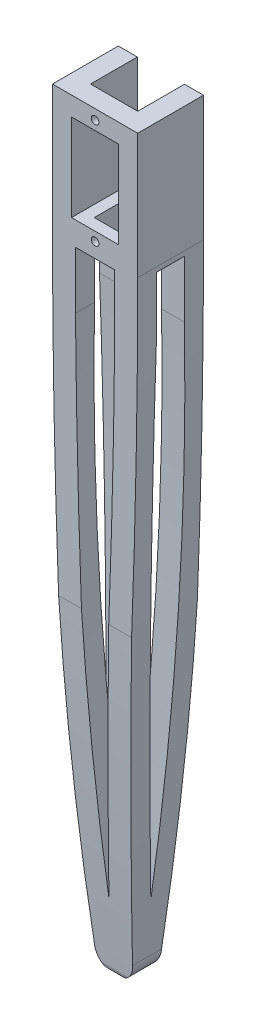
SolidWorks part; units mm, degrees
ref_plane "Front Plane" through (0, 0, 0) normal (0, 0, 1) x (1, 0, 0)
ref_plane "Top Plane" through (0, 0, 0) normal (0, 1, 0) x (1, 0, 0)
ref_plane "Right Plane" through (0, 0, 0) normal (1, 0, 0) x (0, 0, -1)
sketch "Sketch1" plane through (0, 0, 0) normal (0, 0, 1) x (1, 0, 0)
  line L0 (0, -16.45) -> (0, -173.55) construction
  line L1 (-6.2, 16.45) -> (6.2, 16.45)
  line L2 (-11.2, 11.45) -> (-11.2, -16.45)
  line L4 (11.2, 11.45) -> (11.2, -16.45)
  line L5 (-11.2, 16.45) -> (11.2, -16.45) construction
  line L6 (-11.2, -16.45) -> (11.2, 16.45) construction
  arc A1 (-5, -178.55) -> (5, -178.55) centre (0, -178.55) ccw
  arc A2 (-11.2, -16.45) -> (-5, -178.55) centre (2110.9653, -16.45) ccw
  arc A3 (11.2, -16.45) -> (5, -178.55) centre (-2110.9653, -16.45) cw
  arc A4 (11.2, 11.45) -> (6.2, 16.45) centre (6.2, 11.45) ccw
  arc A5 (-6.2, 16.45) -> (-11.2, 11.45) centre (-6.2, 11.45) ccw
  point P0 (0, 0)
  dimension "D4" = 5
  dimension "D1" = 32.9
  dimension "D2" = 22.4
  dimension "D3" = 162.1
extrude "Boss-Extrude2" add sketch "Sketch1" along normal blind 5
sketch "Sketch4" plane through (0, 0, 5) normal (0, 0, 1) x (1, 0, 0)
  line L1 (-6.2, 11.45) -> (6.2, 11.45)
  line L2 (-6.2, 11.45) -> (-6.2, -11.45)
  line L3 (-6.2, -11.45) -> (6.2, -11.45)
  line L4 (6.2, 11.45) -> (6.2, -11.45)
  line L5 (-6.2, 11.45) -> (6.2, -11.45) construction
  line L6 (-6.2, -11.45) -> (6.2, 11.45) construction
  point P0 (0, 0)
  dimension "D1" = 22.9
  dimension "D2" = 12.4
extrude "Cut-Extrude1" cut sketch "Sketch4" against normal blind 5
sketch "Sketch5" plane through (0, 0, 5) normal (0, 0, 1) x (1, 0, 0)
  line L0 (0, 0) -> (0, 13.8) construction
  line L1 (0, 0) -> (0, -13.8) construction
  circle A0 centre (0, 13.8) radius 1
  circle A1 centre (0, -13.8) radius 1
  dimension "D1" = 13.8
  dimension "D2" = 13.8
extrude "Cut-Extrude2" cut sketch "Sketch5" against normal blind 5
sketch3d "3DSketch1"
  line L6 (-5.1604, -32.6864, 5) -> (5.1604, -32.6864, 5)
  spline S2 degree 5 poles (-5.1604, -32.6864, 5) (-5.1261, -37.5289, 5) (-5.0708, -42.3713, 5) (-4.9981, -47.2135, 5) (-4.7659, -60.1446, 5) (-4.4569, -73.0738, 5) (-4.2293, -81.1606, 5) (-3.6967, -97.3316, 5) (-2.9925, -113.496, 5) (-2.6018, -121.5766, 5) (-1.8933, -135.0415, 5) (-1.1015, -148.5022, 5) (-0.7667, -153.8853, 5) (-0.4048, -159.3358, 5) (-0.0148, -164.7842, 5) (-0.0099, -164.8531, 5) (-0.0049, -164.922, 5) (0, -164.9909, 5) knots 0.10922 0.10922 0.10922 0.10922 0.10922 0.10922 0.272094 0.272094 0.272094 0.544187 0.544187 0.544187 0.816281 0.816281 0.816281 0.997676 0.997676 0.997676 1 1 1 1 1 1
  spline S3 degree 5 poles (0, -164.9909, 5) (0.0049, -164.922, 5) (0.0099, -164.8531, 5) (0.0148, -164.7842, 5) (0.4048, -159.3358, 5) (0.7667, -153.8853, 5) (1.1015, -148.5022, 5) (1.8933, -135.0415, 5) (2.6018, -121.5766, 5) (2.9925, -113.496, 5) (3.6967, -97.3316, 5) (4.2293, -81.1606, 5) (4.4569, -73.0738, 5) (4.7659, -60.1446, 5) (4.9981, -47.2135, 5) (5.0708, -42.3713, 5) (5.1261, -37.5289, 5) (5.1604, -32.6864, 5) knots 0 0 0 0 0 0 0.002324 0.002324 0.002324 0.183719 0.183719 0.183719 0.455813 0.455813 0.455813 0.727906 0.727906 0.727906 0.89078 0.89078 0.89078 0.89078 0.89078 0.89078
extrude "Cut-Extrude3" cut sketch "3DSketch1" along direction (0, 0, -1) on the side against the normal blind 5
sketch "Sketch6" plane through (0, 0, 0) normal (0, 0, -1) x (-1, 0, 0)
  line L0 (0, 0) -> (-11.2, 0) construction
  line L1 (-11.2, -16.45) -> (-11.2, 11.45) construction
  line L2 (0, 0) -> (11.2, 0) construction
  line L3 (11.2, 11.45) -> (11.2, -16.45) construction
  line L4 (-11.2, 3.2511) -> (-6.2, 3.2511) construction
  line L5 (-6.2, -11.45) -> (-6.2, 11.45) construction
  line L6 (-8.7, 3.2511) -> (-8.7, 0) construction
  line L7 (6.2, 3.2511) -> (11.2, 3.2511) construction
  line L8 (6.2, 11.45) -> (6.2, -11.45) construction
  line L9 (8.7, 3.2511) -> (8.7, 0) construction
  line L11 (-11.2, 11.45) -> (-6.2, 11.45)
  line L12 (-11.2, 11.45) -> (-11.2, -11.45)
  line L13 (-11.2, -11.45) -> (-6.2, -11.45)
  line L14 (-6.2, 11.45) -> (-6.2, -11.45)
  line L15 (-11.2, 11.45) -> (-6.2, -11.45) construction
  line L16 (-11.2, -11.45) -> (-6.2, 11.45) construction
  line L17 (6.2, 11.45) -> (11.2, 11.45)
  line L18 (6.2, 11.45) -> (6.2, -11.45)
  line L19 (6.2, -11.45) -> (11.2, -11.45)
  line L20 (11.2, 11.45) -> (11.2, -11.45)
  line L21 (6.2, 11.45) -> (11.2, -11.45) construction
  line L22 (6.2, -11.45) -> (11.2, 11.45) construction
  dimension "D1" = 22.9
  dimension "D2" = 22.9
extrude "Boss-Extrude3" add sketch "Sketch6" along normal blind 12.3
sketch "Sketch7" plane through (0, 0, -12.3) normal (0, 0, -1) x (-1, 0, 0)
  line L0 (8.8805, 0) -> (8.8805, 6) construction
  circle A0 centre (-8.6658, 0) radius 1
  circle A1 centre (8.8805, 0) radius 1
  circle A2 centre (8.8805, 6) radius 1
  dimension "D1" = 6
extrude "Cut-Extrude4" cut sketch "Sketch7" against normal blind 5
sketch "Sketch8" plane through (0, 0, 0) normal (0, 0, -1) x (-1, 0, 0)
  line L15 (11.2, -16.45) -> (11.2, -11.45)
  line L16 (11.2, -11.45) -> (6.2, -11.45)
  line L17 (6.2, -11.45) -> (-6.2, -11.45)
  line L18 (-6.2, -11.45) -> (-11.2, -11.45)
  line L19 (-11.2, -11.45) -> (-11.2, -16.45)
  line L20 (11.2, -16.45) -> (11.2, -11.45)
  line L21 (11.2, -11.45) -> (6.2, -11.45)
  line L22 (6.2, -11.45) -> (-6.2, -11.45)
  line L23 (-6.2, -11.45) -> (-11.2, -11.45)
  line L24 (-11.2, -11.45) -> (-11.2, -16.45)
  arc A9 (-11.2, -16.45) -> (-5, -178.55) centre (2110.9653, -16.45) ccw
  arc A10 (-5, -178.55) -> (5, -178.55) centre (0, -178.55) ccw
  arc A11 (5, -178.55) -> (11.2, -16.45) centre (-2110.9653, -16.45) ccw
  arc A12 (-11.2, -16.45) -> (-5, -178.55) centre (2110.9653, -16.45) ccw
  arc A13 (-5, -178.55) -> (5, -178.55) centre (0, -178.55) ccw
  arc A14 (5, -178.55) -> (11.2, -16.45) centre (-2110.9653, -16.45) ccw
  dimension "D1" = 0
extrude "Boss-Extrude4" add sketch "Sketch8" along normal up to surface (12.3 mm away) up to face at (7.6658, 0, -12.3)
sketch "Sketch10" plane through (0, 0, 0) normal (0, 0, 1) x (1, 0, 0)
  line L2 (5.1604, -32.6864) -> (-5.1604, -32.6864)
  line L3 (5.1604, -32.6864) -> (-5.1604, -32.6864)
  spline S4 degree 5 poles (2742.061, 925.339) (1124.3728, 747.4592) (298.2396, 555.4175) (6.2629, 354.0921) (-9.5551, 140.2539) (-4.4569, -73.0738) (-4.2293, -81.1606) (-3.6967, -97.3316) (-2.9925, -113.496) (-2.6018, -121.5766) (-1.8933, -135.0415) (-1.1015, -148.5022) (-0.7667, -153.8853) (8.5195, -293.7189) (36.2296, -432.1823) (-203.7971, -585.1501) (-996.0841, -778.6215) (2070.6534, 438.815) knots -6.632632 -6.632632 -6.632632 -6.632632 -6.632632 -6.632632 0.272094 0.272094 0.272094 0.544187 0.544187 0.544187 0.816281 0.816281 0.816281 0.997676 0.997676 0.997676 5.529664 5.529664 5.529664 5.529664 5.529664 5.529664 only from (-5.1604, -32.6864) to (0, -164.9909)
  spline S5 degree 5 poles (-2591.2367, -1178.5003) (505.7514, -640.2869) (94.1134, -500.1546) (-26.7405, -381.6628) (-6.8269, -268.2322) (0.7667, -153.8853) (1.1015, -148.5022) (1.8933, -135.0415) (2.6018, -121.5766) (2.9925, -113.496) (3.6967, -97.3316) (4.2293, -81.1606) (4.4569, -73.0738) (9.5551, 140.2541) (-6.2629, 354.0925) (-298.2404, 555.4181) (-1124.376, 747.46) (-2742.0685, 925.3399) knots -3.670581 -3.670581 -3.670581 -3.670581 -3.670581 -3.670581 0.002324 0.002324 0.002324 0.183719 0.183719 0.183719 0.455813 0.455813 0.455813 0.727906 0.727906 0.727906 7.632639 7.632639 7.632639 7.632639 7.632639 7.632639 only from (0, -164.9909) to (5.1604, -32.6864)
  spline S6 degree 5 poles (-5.1604, -32.6864) (-5.1261, -37.5289) (-5.0708, -42.3713) (-4.9981, -47.2135) (-4.7659, -60.1446) (-4.4569, -73.0738) (-4.2293, -81.1606) (-3.6967, -97.3316) (-2.9925, -113.496) (-2.6018, -121.5766) (-1.8933, -135.0415) (-1.1015, -148.5022) (-0.7667, -153.8853) (-0.4048, -159.3358) (-0.0148, -164.7842) (-0.0099, -164.8531) (-0.0049, -164.922) (0, -164.9909) knots 0.10922 0.10922 0.10922 0.10922 0.10922 0.10922 0.272094 0.272094 0.272094 0.544187 0.544187 0.544187 0.816281 0.816281 0.816281 0.997676 0.997676 0.997676 1 1 1 1 1 1
  spline S7 degree 5 poles (0, -164.9909) (0.0049, -164.922) (0.0099, -164.8531) (0.0148, -164.7842) (0.4048, -159.3358) (0.7667, -153.8853) (1.1015, -148.5022) (1.8933, -135.0415) (2.6018, -121.5766) (2.9925, -113.496) (3.6967, -97.3316) (4.2293, -81.1606) (4.4569, -73.0738) (4.7659, -60.1446) (4.9981, -47.2135) (5.0708, -42.3713) (5.1261, -37.5289) (5.1604, -32.6864) knots 0 0 0 0 0 0 0.002324 0.002324 0.002324 0.183719 0.183719 0.183719 0.455813 0.455813 0.455813 0.727906 0.727906 0.727906 0.89078 0.89078 0.89078 0.89078 0.89078 0.89078
  dimension "D1" = 0
extrude "Cut-Extrude5" cut sketch "Sketch10" against normal blind 121
sketch "Sketch12" plane through (0, 0, 0) normal (1, 0, 0) x (0, 0, -1)
  line L2 (3.65, -183.55) -> (3.65, -164.9909) construction
  line L3 (-5, -183.55) -> (12.3, -183.55) construction
  line L6 (0, -32.6864) -> (7.3, -32.6864)
  line L7 (3.65, -32.6864) -> (3.65, -164.9909) construction
  arc A0 (0, -32.6864) -> (3.65, -164.9909) centre (1196.4285, -65.8821) ccw
  arc A1 (7.3, -32.6864) -> (3.65, -164.9909) centre (-1189.1285, -65.8821) cw
extrude "Cut-Extrude7" cut sketch "Sketch12" against normal through all
sketch "Sketch14" plane through (0, 0, 0) normal (1, 0, 0) x (0, 0, -1)
  line L0 (7.3, -32.6864) -> (0, -32.6864)
  arc A0 (7.3, -32.6864) -> (3.65, -164.9909) centre (-1189.1285, -65.8821) cw
  arc A1 (0, -32.6864) -> (3.65, -164.9909) centre (1196.4285, -65.8821) ccw
extrude "Cut-Extrude8" cut sketch "Sketch14" along normal blind 121
sketch "Sketch15" plane through (0, 0, 0) normal (1, 0, 0) x (0, 0, -1)
  line L6 (12.3019, -32.6864) -> (24.1567, -32.6864)
  line L7 (24.1567, -32.6864) -> (24.1567, -183.55)
  line L8 (24.1567, -183.55) -> (5.6261, -183.55)
  line L9 (-5.0019, -32.6864) -> (-15.6441, -32.6864)
  line L10 (-15.6441, -32.6864) -> (-15.6441, -183.55)
  line L11 (1.6739, -183.55) -> (-15.6441, -183.55)
  arc A2 (12.3019, -32.6864) -> (7.1191, -182.1952) centre (-1189.1285, -65.8821) cw
  arc A3 (-5.0019, -32.6864) -> (0.1809, -182.1952) centre (1196.4285, -65.8821) ccw
  arc A6 (5.6261, -183.55) -> (7.1191, -182.1952) centre (5.6261, -182.05) ccw
  arc A7 (1.6739, -183.55) -> (0.1809, -182.1952) centre (1.6739, -182.05) cw
  dimension "D2" = 1.5
extrude "Cut-Extrude12" cut sketch "Sketch15" against normal mid plane 121
sketch "Sketch16" plane through (0, -11.45, 0) normal (0, 1, 0) x (1, 0, 0)
  line L8 (-3.2, -2) -> (3.2, -2)
  line L9 (3.2, -2) -> (3.2, 9.3)
  line L10 (3.2, 9.3) -> (-3.2, 9.3)
  line L11 (-3.2, 9.3) -> (-3.2, -2)
  line L12 (-3.2, -2) -> (3.2, -2)
  line L13 (3.2, -2) -> (3.2, 9.3)
  line L14 (3.2, 9.3) -> (-3.2, 9.3)
  line L15 (-3.2, 9.3) -> (-3.2, -2)
  dimension "D1" = 3
extrude "Cut-Extrude13" cut sketch "Sketch16" against normal up to surface (21.2364 mm away) contours L12 L13 L14 L15
sketch "Sketch21" plane through (0, 0, 5) normal (0, 0, 1) x (1, 0, 0)
  line L0 (5.1604, -32.6864) -> (-5.1604, -32.6864) construction
  line L1 (0, -32.6864) -> (0, -17.6864) construction
  line L3 (-5.1604, -32.6864) -> (5.1604, -32.6864)
  line L4 (-5.1604, -32.6864) -> (-5.1604, -17.6864)
  line L5 (-5.1604, -17.6864) -> (5.1604, -17.6864)
  line L6 (5.1604, -32.6864) -> (5.1604, -17.6864)
  dimension "D1" = 15
extrude "Cut-Extrude14" cut sketch "Sketch21" against normal through all
sketch "Sketch23" plane through (-5.1604, 0, 0) normal (1, 0, 0) x (0, 0, -1)
  line L1 (0, -32.6864) -> (7.3, -32.6864)
  line L2 (0, -32.6864) -> (0, -17.6864)
  line L3 (0, -17.6864) -> (7.3, -17.6864)
  line L4 (7.3, -32.6864) -> (7.3, -17.6864)
  dimension "D1" = 15
extrude "Cut-Extrude15" cut sketch "Sketch23" against normal through all both and the other way through all
sketch "Sketch24" plane through (0, 11.45, 0) normal (0, 1, 0) x (1, 0, 0)
  line L1 (6.2, 0) -> (11.2, 0)
  line L2 (6.2, 0) -> (6.2, 12.3)
  line L3 (6.2, 12.3) -> (11.2, 12.3)
  line L4 (11.2, 0) -> (11.2, 12.3)
  line L5 (-6.2, 0) -> (-11.2, 0)
  line L6 (-6.2, 0) -> (-6.2, 12.3)
  line L7 (-6.2, 12.3) -> (-11.2, 12.3)
  line L8 (-11.2, 0) -> (-11.2, 12.3)
extrude "Boss-Extrude5" add sketch "Sketch24" along normal up to surface (5 mm away) up to face at (0, 16.45, 2.5)
sketch "Sketch25" plane through (11.2, 0, 0) normal (1, 0, 0) x (0, 0, -1)
  line L1 (-5, 11.45) -> (12.3, 11.45)
  line L2 (-5, 11.45) -> (-5, 16.45)
  line L3 (-5, 16.45) -> (12.3, 16.45)
  line L4 (12.3, 11.45) -> (12.3, 16.45)
extrude "Boss-Extrude6" add sketch "Sketch25" against normal up to next
sketch "Sketch26" plane through (-11.2, 0, 0) normal (-1, 0, 0) x (0, 0, 1)
  line L1 (5, 11.45) -> (0, 11.45)
  line L2 (5, 11.45) -> (5, 16.45)
  line L3 (5, 16.45) -> (0, 16.45)
  line L4 (0, 11.45) -> (0, 16.45)
extrude "Boss-Extrude7" add sketch "Sketch26" against normal up to next
